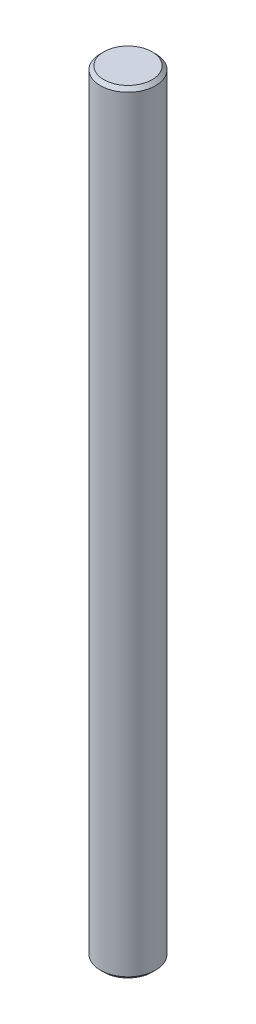
SolidWorks part; units mm, degrees
ref_plane "Front Plane" through (0, 0, 0) normal (0, 0, 1) x (1, 0, 0)
ref_plane "Top Plane" through (0, 0, 0) normal (0, 1, 0) x (1, 0, 0)
ref_plane "Right Plane" through (0, 0, 0) normal (1, 0, 0) x (0, 0, -1)
sketch "Sketch1" plane through (0, 0, 0) normal (0, 1, 0) x (1, 0, 0)
  circle A0 centre (0, 0) radius 4
  dimension "D1" = 8
extrude "Boss-Extrude1" add sketch "Sketch1" along normal blind 112
chamfer "Chamfer1" distance 0.5 angle 45 2 edges at (0, 0, 4) (0, 112, 4)
